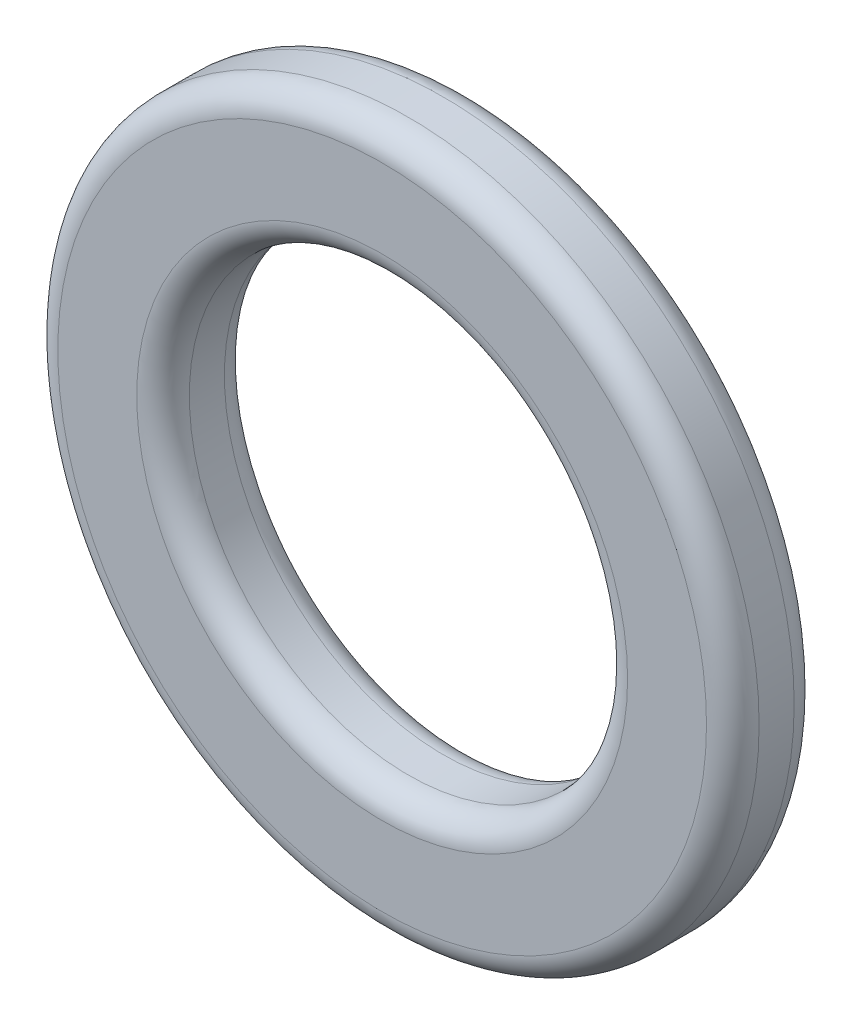
SolidWorks part; units mm, degrees
material "Gomma naturale"
ref_plane "Piano frontale" through (0, 0, 0) normal (0, 0, 1) x (1, 0, 0)
ref_plane "Piano superiore" through (0, 0, 0) normal (0, 1, 0) x (1, 0, 0)
ref_plane "Piano destro" through (0, 0, 0) normal (1, 0, 0) x (0, 0, -1)
sketch "Schizzo1" plane through (0, 0, 0) normal (0, 0, 1) x (1, 0, 0)
  circle A0 centre (0, 0) radius 2.5
  circle A1 centre (0, 0) radius 4
  dimension "D1" = 5
  dimension "D2" = 8
extrude "Estrusione-Estrusione1" add sketch "Schizzo1" along normal blind 1
fillet "Raccordo1" radius 0.3 4 edges at (2.5, 0, 0) (4, 0, 0) (2.5, 0, 1) (4, 0, 1)
